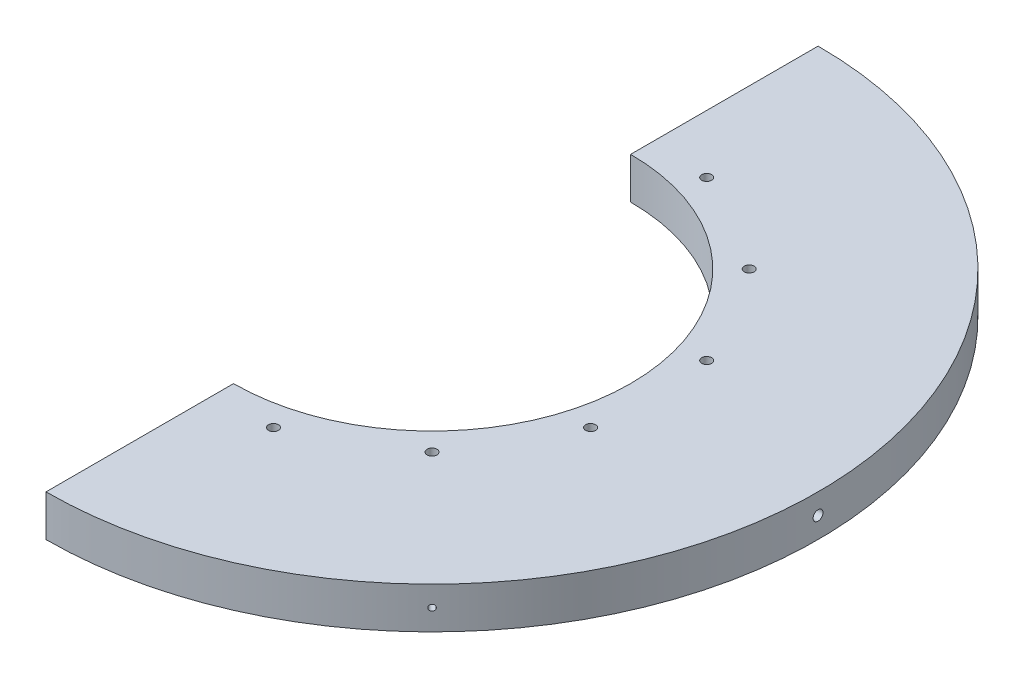
SolidWorks part; units mm, degrees
material "6061-T6 (SS)"
ref_plane "Front Plane" through (0, 0, 0) normal (0, 0, 1) x (1, 0, 0)
ref_plane "Top Plane" through (0, 0, 0) normal (0, 1, 0) x (1, 0, 0)
ref_plane "Right Plane" through (0, 0, 0) normal (1, 0, 0) x (0, 0, -1)
sketch "Sketch1" plane through (0, 0, 0) normal (0, 1, 0) x (1, 0, 0)
  circle A0 centre (0, 0) radius 88.9
  dimension "D1" = 177.8
extrude "Boss-Extrude1" add sketch "Sketch1" along normal blind 9.525
sketch "Sketch2" plane through (0, 9.525, 0) normal (0, 1, 0) x (1, 0, 0)
  circle A0 centre (0, 0) radius 45.72
extrude "Cut-Extrude1" cut sketch "Sketch2" against normal blind 12.7
sketch "Sketch3" plane through (0, 9.525, 0) normal (0, 1, 0) x (1, 0, 0)
  line L0 (0, 0) -> (0, 131.3286) construction
  line L1 (0, 0) -> (35.2548, 131.5728) construction
  circle A1 centre (13.3649, 49.8787) radius 1.143
  dimension "D2" = 51.6382
  dimension "D1" = 2.286
  dimension "D3" = 15
extrude "Cut-Extrude2" cut sketch "Sketch3" against normal blind 12.7
sketch "Sketch5" plane through (0, 9.525, 0) normal (0, 1, 0) x (1, 0, 0)
  line L0 (0, 139.1256) -> (0, -130.5388)
  line L1 (0, -130.5388) -> (-200.055, 4.2934)
  line L2 (-200.055, 4.2934) -> (0, 139.1256)
extrude "Cut-Extrude3" cut sketch "Sketch5" against normal through all both and the other way through all
pattern_circular "CirPattern1" count 12 over 360 about axis through (0, 9.525, 0) along (0, 1, 0) of "Cut-Extrude2"
ref_plane "Plane1" through (88.9, 0, 0) normal (1, 0, 0) x (0, 0, -1)
sketch "Sketch6" plane through (88.9, 0, 0) normal (1, 0, 0) x (0, 0, -1)
  line L0 (0, 0) -> (0, 9.652) construction
  circle A0 centre (0, 4.826) radius 1.143
  dimension "D2" = 2.286
  dimension "D1" = 9.652
extrude "Cut-Extrude4" cut sketch "Sketch6" against normal blind 25.4
ref_plane "Plane2" through (62.8618, 0, 62.8618) normal (0.7071, 0, 0.7071) x (0, -1, 0)
sketch "Sketch7" plane through (62.8618, 0, 62.8618) normal (0.7071, 0, 0.7071) x (0, -1, 0)
  line L0 (0, 0) -> (-9.652, 0) construction
  circle A0 centre (-4.826, 0) radius 0.6985
  dimension "D2" = 1.397
  dimension "D1" = 9.652
extrude "Cut-Extrude5" cut sketch "Sketch7" against normal blind 3.175
pattern_circular "CirPattern2" count 4 over 360 about axis through (0, 9.525, 0) along (0, 1, 0) of "Cut-Extrude5"
